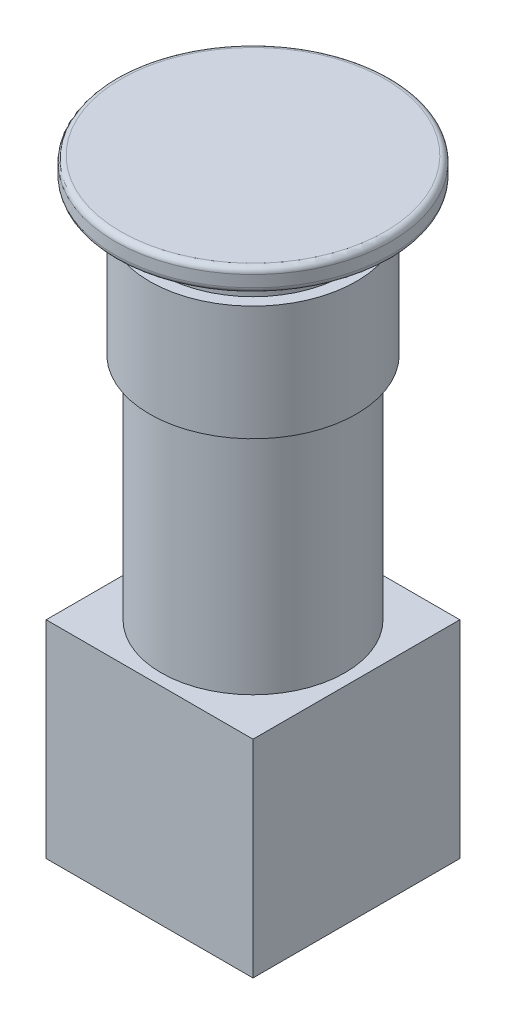
SolidWorks part; units mm, degrees
ref_plane "Plan de face" through (0, 0, 0) normal (0, 0, 1) x (1, 0, 0)
ref_plane "Plan de dessus" through (0, 0, 0) normal (0, 1, 0) x (1, 0, 0)
ref_plane "Plan de droite" through (0, 0, 0) normal (1, 0, 0) x (0, 0, -1)
sketch "Esquisse1" plane through (0, 0, 0) normal (0, 1, 0) x (1, 0, 0)
  line L1 (-9, 9) -> (9, 9)
  line L2 (-9, 9) -> (-9, -9)
  line L3 (-9, -9) -> (9, -9)
  line L4 (9, 9) -> (9, -9)
  dimension "D1" = 18
  dimension "D2" = 18
  dimension "D3" = 9
  dimension "D4" = 9
extrude "Boss.-Extru.1" add sketch "Esquisse1" along normal blind 18
sketch "Esquisse2" plane through (0, 18, 0) normal (0, 1, 0) x (1, 0, 0)
  circle A0 centre (0, 0) radius 8
  dimension "D1" = 16
extrude "Boss.-Extru.2" add sketch "Esquisse2" along normal blind 20
sketch "Esquisse3" plane through (0, 38, 0) normal (0, 1, 0) x (1, 0, 0)
  circle A0 centre (0, 0) radius 9
  dimension "D1" = 18
extrude "Boss.-Extru.3" add sketch "Esquisse3" along normal blind 10
sketch "Esquisse4" plane through (0, 48, 0) normal (0, 1, 0) x (1, 0, 0)
  circle A0 centre (0, 0) radius 8
  dimension "D1" = 16
extrude "Boss.-Extru.4" add sketch "Esquisse4" along normal blind 3
sketch "Esquisse5" plane through (0, 51, 0) normal (0, 1, 0) x (1, 0, 0)
  circle A0 centre (0, 0) radius 12
extrude "Boss.-Extru.5" add sketch "Esquisse5" along normal blind 2
fillet "Congé1" radius 0.5 1 edges at (0, 53, 12)
fillet "Congé2" radius 0.5 1 edges at (0, 51, 12)
